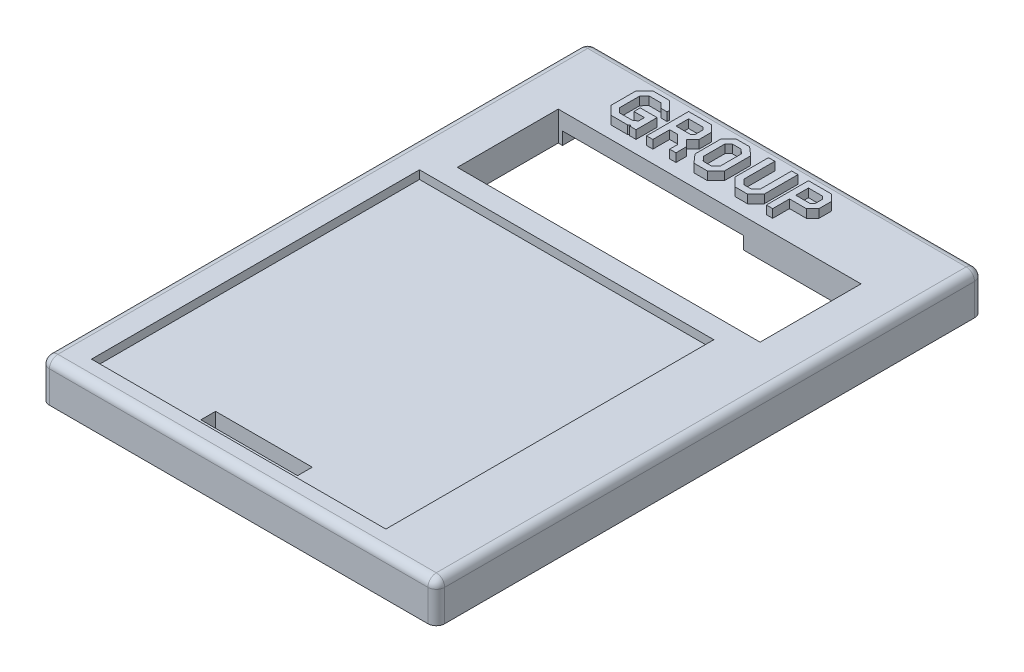
SolidWorks part; units mm, degrees
ref_plane "Front Plane" through (0, 0, 0) normal (0, 0, 1) x (1, 0, 0)
ref_plane "Top Plane" through (0, 0, 0) normal (0, 1, 0) x (1, 0, 0)
ref_plane "Right Plane" through (0, 0, 0) normal (1, 0, 0) x (0, 0, -1)
ref_plane "Plane1" through (0, 7, 0) normal (0, 1, 0) x (1, 0, 0)
sketch "Sketch1" plane through (0, 7, 0) normal (0, 1, 0) x (1, 0, 0)
  line L0 (0, 130) -> (0, 0)
  line L1 (0, 0) -> (94, 0)
  line L2 (94, 0) -> (94, 130)
  line L3 (94, 130) -> (0, 130)
extrude "Boss-Extrude1" add sketch "Sketch1" against normal blind 9.5
sketch "Sketch2" plane through (0, -2.5, 0) normal (0, -1, 0) x (1, 0, 0)
  line L0 (1.75, -128.25) -> (92.25, -128.25)
  line L1 (92.25, -128.25) -> (92.25, -1.75)
  line L2 (92.25, -1.75) -> (1.75, -1.75)
  line L3 (1.75, -1.75) -> (1.75, -128.25)
extrude "Cut-Extrude1" cut sketch "Sketch2" against normal blind 2.5
sketch "Sketch3" plane through (0, 0, 0) normal (0, -1, 0) x (1, 0, 0)
  line L0 (83, -88) -> (11, -88)
  line L1 (11, -88) -> (11, -112)
  line L2 (11, -112) -> (83, -112)
  line L3 (83, -112) -> (83, -88)
extrude "Cut-Extrude2" cut sketch "Sketch3" against normal through all
sketch "Sketch4" plane through (0, 7, 0) normal (0, 1, 0) x (-1, 0, 0)
  line L0 (-77, -83) -> (-7, -83)
  line L1 (-7, -83) -> (-7, -5)
  line L2 (-7, -5) -> (-77, -5)
  line L3 (-77, -5) -> (-77, -83)
extrude "Cut-Extrude3" cut sketch "Sketch4" against normal blind 2
sketch "Sketch5" plane through (0, 5, 0) normal (0, 1, 0) x (-1, 0, 0)
  line L0 (-30.5, -7.5) -> (-53.5, -7.5)
  line L1 (-53.5, -7.5) -> (-53.5, -11)
  line L2 (-53.5, -11) -> (-30.5, -11)
  line L3 (-30.5, -11) -> (-30.5, -7.5)
extrude "Cut-Extrude4" cut sketch "Sketch5" against normal through all
sketch "Sketch6" plane through (0, 0, 0) normal (0, -1, 0) x (1, 0, 0)
  line L0 (83, -109) -> (89, -109)
  line L1 (89, -109) -> (89, -91)
  line L2 (89, -91) -> (83, -91)
  line L3 (83, -91) -> (83, -109)
extrude "Cut-Extrude5" cut sketch "Sketch6" against normal blind 3.5
sketch "Sketch7" plane through (0, 0, 0) normal (0, -1, 0) x (1, 0, 0)
  line L0 (12, -112) -> (12, -119.5)
  line L1 (12, -119.5) -> (55, -119.5)
  line L2 (55, -119.5) -> (55, -112)
  line L3 (55, -112) -> (12, -112)
extrude "Cut-Extrude6" cut sketch "Sketch7" against normal blind 3
fillet "Fillet1" radius 2 8 edges at (0, 2.25, 0) (0, 2.25, -130) (0, 7, -65) (94, 2.25, 0) (47, 7, 0) (47, 7, -130) (94, 7, -65) (94, 2.25, -130)
sketch "Sketch10" plane through (0, 7, 0) normal (0, 1, 0) x (1, 0, 0)
  line L52 (26.5, 123) -> (24.5, 125)
  line L53 (20.5, 125) -> (24.5, 125)
  line L54 (18.5, 123) -> (18.5, 117)
  line L55 (20.5, 115) -> (24.5, 115)
  line L56 (26.5, 123) -> (26.5, 122.3787)
  line L57 (20.5, 125) -> (18.5, 123)
  line L58 (18.5, 117) -> (20.5, 115)
  line L59 (24.5, 115) -> (25, 115.3091)
  line L60 (24.0738, 116.5) -> (25, 117.0727)
  line L68 (21.1109, 123.5) -> (23.8787, 123.5)
  line L69 (20, 122.3678) -> (20, 117.6213)
  line L70 (21.1213, 116.5) -> (24.0738, 116.5)
  line L71 (25, 118.5) -> (25, 117.0727)
  line L72 (20, 117.6213) -> (21.1213, 116.5)
  line L73 (20, 122.3678) -> (21.1109, 123.5)
  line L74 (25, 122.3787) -> (23.8787, 123.5)
  line L75 (25, 122.3787) -> (26.5, 122.3787)
  line L78 (25, 115.3091) -> (25, 115)
  line L79 (25, 115) -> (26.5, 115)
  line L82 (22.5, 120) -> (22.5, 118.5)
  line L83 (22.5, 118.5) -> (25, 118.5)
  line L84 (32.3787, 119) -> (30.5, 119)
  line L85 (29, 125) -> (34.5, 125)
  line L86 (29, 125) -> (29, 115)
  line L87 (29, 115) -> (30.5, 115)
  line L88 (36, 123.5) -> (36, 120.5)
  line L89 (34.5, 125) -> (36, 123.5)
  line L90 (36, 120.5) -> (34.5, 119)
  line L91 (30.5, 119) -> (30.5, 115)
  line L92 (30.5, 123.4962) -> (30.5, 120.5)
  line L93 (30.5, 120.5) -> (33.8825, 120.5)
  line L94 (33.8825, 120.5) -> (34.5, 121.1175)
  line L95 (34.5, 121.1175) -> (34.5, 122.8787)
  line L96 (34.5, 122.8787) -> (33.8825, 123.4962)
  line L97 (33.8825, 123.4962) -> (30.5, 123.4962)
  line L98 (34.5, 119) -> (36, 117.5)
  line L99 (34.5, 115) -> (34.5, 116.8787)
  line L100 (32.3787, 119) -> (34.5, 116.8787)
  line L101 (36, 117.5) -> (36, 115)
  line L102 (34.5, 115) -> (36, 115)
  line L103 (43.5, 125) -> (45.5, 123.2761)
  line L104 (40.272, 125) -> (43.5, 125)
  line L105 (38.5, 123.2761) -> (38.5, 117.0214)
  line L106 (40.272, 115) -> (43.5, 115)
  line L107 (45.5, 123.2761) -> (45.5, 117.0214)
  line L108 (45.5, 117.0214) -> (43.5, 115)
  line L109 (40.272, 115) -> (38.5, 117.0214)
  line L110 (38.5, 123.2761) -> (40.272, 125)
  line L111 (42.9427, 123.5) -> (44, 122.5887)
  line L112 (44, 122.5887) -> (44, 117.638)
  line L113 (44, 117.638) -> (42.874, 116.5)
  line L114 (40.9518, 116.5) -> (42.874, 116.5)
  line L115 (40.9518, 116.5) -> (40, 117.5858)
  line L116 (40, 122.6426) -> (40, 117.5858)
  line L117 (40, 122.6426) -> (40.8813, 123.5)
  line L118 (40.8813, 123.5) -> (42.9427, 123.5)
  line L119 (48, 117) -> (50, 115)
  line L120 (48, 125) -> (49.5, 125)
  line L121 (48, 125) -> (48, 117)
  line L122 (50, 115) -> (53, 115)
  line L123 (55, 125) -> (55, 117)
  line L124 (53, 115) -> (55, 117)
  line L126 (53.5, 123.5) -> (53.5, 117.6213)
  line L127 (52.3787, 116.5) -> (53.5, 117.6213)
  line L128 (50.6213, 116.5) -> (52.3787, 116.5)
  line L129 (49.5, 117.6213) -> (50.6213, 116.5)
  line L130 (49.5, 123.5) -> (49.5, 117.6213)
  line L131 (49.5, 123.5) -> (49.5, 125)
  line L132 (53.5, 123.5) -> (53.5, 125)
  line L133 (53.5, 125) -> (55, 125)
  line L134 (49.5, 123.5) -> (53.5, 123.5) construction
  line L135 (92, 128) -> (2, 128) construction
  line L136 (48, 125) -> (55, 125) construction
  line L149 (63, 119) -> (59, 119)
  line L150 (57.5, 125) -> (63, 125)
  line L151 (57.5, 125) -> (57.5, 115)
  line L152 (57.5, 115) -> (59, 115)
  line L153 (64.5, 123.5) -> (64.5, 120.5)
  line L154 (59, 119) -> (59, 115)
  line L155 (59, 123.5) -> (59, 120.5)
  line L156 (59, 120.5) -> (62.3787, 120.5)
  line L157 (62.3787, 120.5) -> (63, 121.1213)
  line L158 (63, 121.1213) -> (63, 122.8787)
  line L159 (63, 122.8787) -> (62.3787, 123.5)
  line L160 (62.3787, 123.5) -> (59, 123.5)
  line L161 (63, 119) -> (64.5, 120.5)
  line L162 (64.5, 123.5) -> (63, 125)
  line L163 (11, 88) -> (11, 112) construction
  line L164 (22.5, 120) -> (26.5, 120)
  line L165 (26.5, 120) -> (26.5, 115)
  point P0 (19.5, 124)
  point P22 (22.5, 115)
  point P79 (63.75, 119.75)
  dimension "D1" = 4
  dimension "D2" = 2
  dimension "D3" = 2
  dimension "D5" = 2
  dimension "D6" = 2
  dimension "D7" = 1.5
  dimension "D8" = 1.5
  dimension "D9" = 1.5
  dimension "D10" = 1.5
  dimension "D11" = 1.5
  dimension "D12" = 1.5
  dimension "D13" = 1.5
  dimension "D14" = 1.5
  dimension "D15" = 7
  dimension "D16" = 1.5
  dimension "D17" = 6
  dimension "D18" = 1.5
  dimension "D19" = 1.5
  dimension "D20" = 1.5
  dimension "D21" = 1.5
  dimension "D22" = 1.5038
  dimension "D23" = 1.5
  dimension "D24" = 1.4973
  dimension "D25" = 1.5
  dimension "D26" = 2.5
  dimension "D27" = 10
  dimension "D28" = 1.8787
  dimension "D29" = 1.5
  dimension "D30" = 1.5
  dimension "D31" = 1.5
  dimension "D32" = 2
  dimension "D33" = 10
  dimension "D34" = 10
  dimension "D35" = 3
  dimension "D36" = 2
  dimension "D37" = 2
  dimension "D38" = 7
  dimension "D39" = 2
  dimension "D40" = 10
  dimension "D41" = 5
  dimension "D42" = 2.5
  dimension "D43" = 1.5
  dimension "D44" = 7
  dimension "D45" = 2.5
  dimension "D46" = 2.5
  dimension "D47" = 1.5
  dimension "D48" = 6
  dimension "D49" = 1.5
  dimension "D50" = 1.5
  dimension "D51" = 4
  dimension "D52" = 1.5
  dimension "D53" = 1.5
  dimension "D54" = 3
  dimension "D55" = 1.7574
  dimension "D56" = 3
  dimension "D57" = 1.5
  dimension "D58" = 1.5
  dimension "D59" = 10
  dimension "D60" = 1.5
  dimension "D61" = 2.5
  dimension "D62" = 5
  dimension "D63" = 7.5
extrude "Boss-Extrude3" add sketch "Sketch10" along normal blind 2
